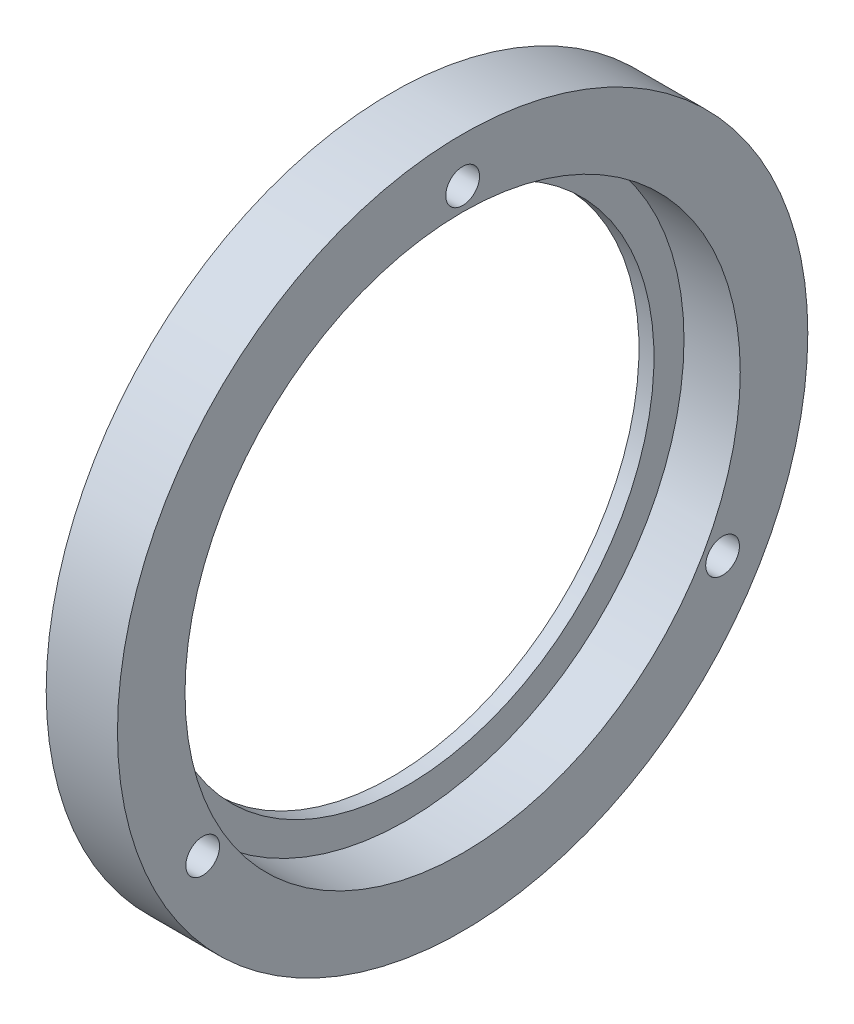
SolidWorks part; units mm, degrees
ref_plane "Plane1" through (0, 0, 0) normal (0, 0, 1) x (1, 0, 0)
ref_plane "Plane2" through (0, 0, 0) normal (0, 1, 0) x (1, 0, 0)
ref_plane "Plane3" through (0, 0, 0) normal (1, 0, 0) x (0, 0, -1)
sketch "Esquisse1" plane through (0, 0, 0) normal (0, 0, 1) x (1, 0, 0)
  line L0 (0, 0) -> (53.975, 0) construction
  line L1 (0, 33) -> (0, 46)
  line L2 (0, 46) -> (9.5, 46)
  line L3 (9.5, 46) -> (9.5, 37)
  line L4 (9.5, 37) -> (2, 37)
  line L5 (2, 37) -> (2, 33)
  line L6 (2, 33) -> (0, 33)
  dimension "D1" = 9.5
  dimension "D2" = 46
  dimension "D3" = 33
  dimension "D4" = 37
  dimension "D5" = 7.5
revolve "Base-Révolution" add sketch "Esquisse1" angle 360 about L0
sketch "Esquisse2" plane through (0, 0, 0) normal (-1, 0, 0) x (0, 0, 1)
  line L0 (0, 0) -> (0, 40) construction
  circle A0 centre (0, 40) radius 2.25
  dimension "D2" = 4.5
  dimension "D1" = 40
extrude "Enlèv. mat.-Extru.1" cut sketch "Esquisse2" against normal through all
pattern_circular "Répétition circulaire1" count 3 every 120 about axis through (0, 0, 0) along (1, 0, 0)
